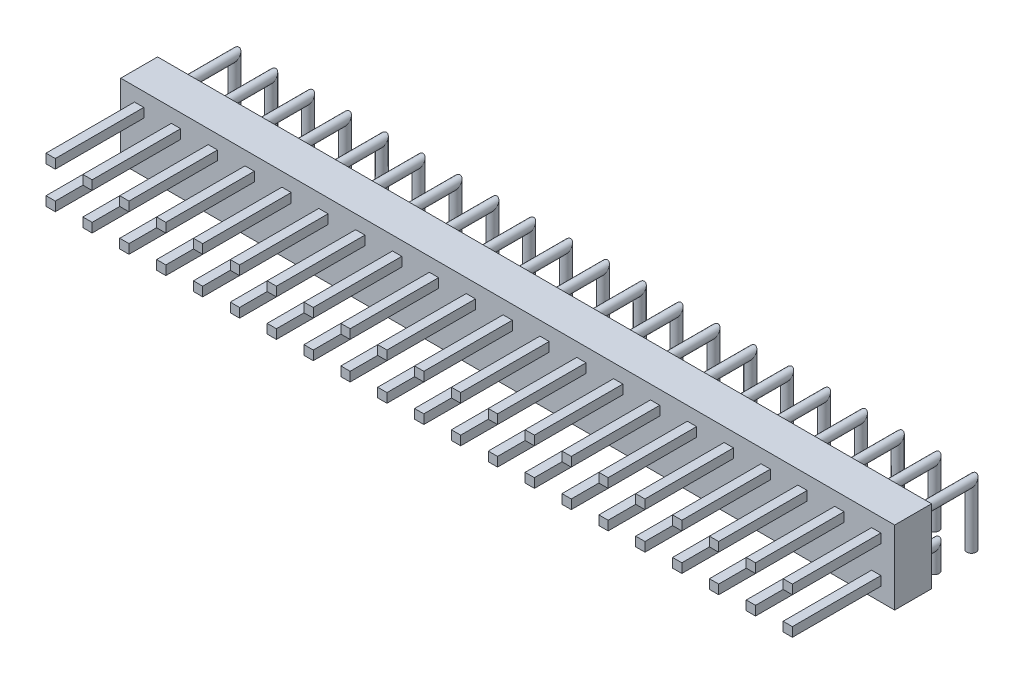
SolidWorks part; units mm, degrees
ref_plane "Front Plane" through (0, 0, 0) normal (0, 0, 1) x (1, 0, 0)
ref_plane "Top Plane" through (0, 0, 0) normal (0, 1, 0) x (1, 0, 0)
ref_plane "Right Plane" through (0, 0, 0) normal (1, 0, 0) x (0, 0, -1)
sketch "Sketch1" plane through (0, 0, 0) normal (0, 0, 1) x (1, 0, 0)
  line L0 (0, 2.54) -> (0, 5.08)
  line L1 (0, 0) -> (2.54, 0)
  line L2 (0, 0) -> (0, 2.54)
  line L3 (0, 2.54) -> (2.54, 2.54)
  line L4 (2.54, 0) -> (2.54, 2.54)
  line L5 (0, 5.08) -> (2.54, 5.08)
  line L6 (2.54, 5.08) -> (2.54, 2.54)
  dimension "D1" = 2.54
  dimension "D2" = 2.54
extrude "Boss-Extrude1" add sketch "Sketch1" along normal blind 2.54 contours L6 L5 L0 L3 | L1 L4 L3 L2
sketch "Sketch2" plane through (0, 0, 2.54) normal (0, 0, 1) x (1, 0, 0)
  line L0 (1.27, 2.54) -> (1.27, 1.59) construction
  line L1 (0.95, 1.59) -> (1.59, 1.59)
  line L2 (0.95, 1.59) -> (0.95, 0.95)
  line L3 (0.95, 0.95) -> (1.59, 0.95)
  line L4 (1.59, 1.59) -> (1.59, 0.95)
  line L6 (2.54, 1.27) -> (1.59, 1.27) construction
  line L9 (2.54, 5.08) -> (2.54, 0) construction
  line L10 (0, 0) -> (2.54, 0) construction
  line L11 (0.95, 4.13) -> (1.59, 4.13)
  line L12 (0.95, 4.13) -> (0.95, 3.49)
  line L13 (0.95, 3.49) -> (1.59, 3.49)
  line L14 (1.59, 4.13) -> (1.59, 3.49)
  point P12 (0.95, 3.81)
  point P13 (1.59, 1.27)
  point P14 (0.95, 1.27)
  point P15 (1.27, 1.59)
  dimension "D1" = 0.64
  dimension "D2" = 1.27
  dimension "D3" = 2.54
  dimension "D4" = 1.27
extrude "Boss-Extrude3" add sketch "Sketch2" along normal blind 6.1
ref_plane "Plane2" through (1.27, 0, 0) normal (1, 0, 0) x (0, 0, -1)
sketch "Sketch14" plane through (1.27, 0, 0) normal (1, 0, 0) x (0, 0, -1)
  line L0 (0, 1.27) -> (1.48, 1.27)
  line L1 (1.48, 1.27) -> (1.48, -0.3)
  line L2 (0, 5.08) -> (0, 0) construction
  line L3 (-2.54, 0) -> (0, 0) construction
  line L4 (-2.54, 5.08) -> (-2.54, 0) construction
  line L5 (0, 3.81) -> (4.02, 3.81)
  line L6 (4.02, 3.81) -> (4.02, -0.3)
  line L7 (-2.54, 5.08) -> (0, 5.08) construction
  dimension "D1" = 1.27
  dimension "D2" = 0.3
  dimension "D3" = 4.02
  dimension "D4" = 2.54
  dimension "D5" = 1.27
sweep "Sweep2" add path "Sketch14" circular profile diameter 0.64 parameters "D3"=0.64
sketch "Sketch21" plane through (1.27, 0, 0) normal (1, 0, 0) x (0, 0, -1)
  line L0 (4.02, 3.81) -> (4.02, -0.3) construction
  line L1 (0, 3.81) -> (4.02, 3.81) construction
  line L2 (4.02, 3.81) -> (4.02, -0.3)
  line L3 (0, 3.81) -> (4.02, 3.81)
sweep "Sweep3" add path "Sketch21" circular profile diameter 0.64 parameters "D3"=0.64
pattern_linear "LPattern1" count 21 spacing 2.54 along (1, 0, 0) of "Boss-Extrude1", "Boss-Extrude3", "Sweep3", "Sweep2"
